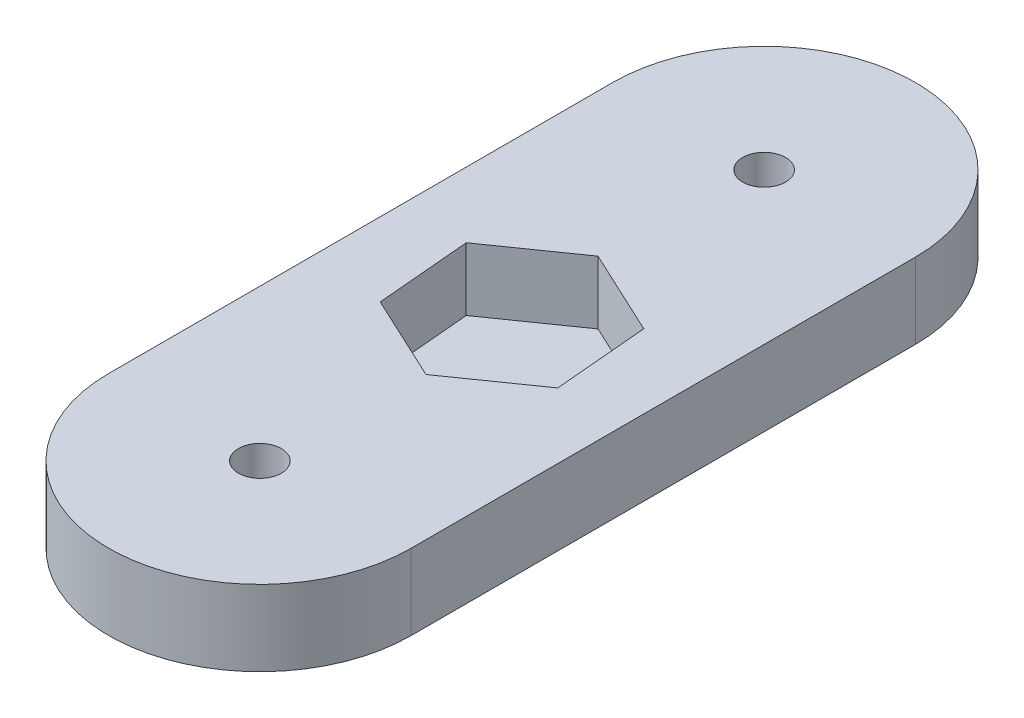
SolidWorks part; units mm, degrees
material "ABS PC"
ref_plane "Front Plane" through (0, 0, 0) normal (0, 0, 1) x (1, 0, 0)
ref_plane "Top Plane" through (0, 0, 0) normal (0, 1, 0) x (1, 0, 0)
ref_plane "Right Plane" through (0, 0, 0) normal (1, 0, 0) x (0, 0, -1)
sketch "Sketch1" plane through (0, 0, 0) normal (0, 1, 0) x (1, 0, 0)
  line L0 (0, 0) -> (0, 40) construction
  line L1 (-12, 0) -> (-12, 40)
  line L2 (12, 0) -> (12, 40)
  arc A0 (-12, 0) -> (12, 0) centre (0, 0) ccw
  arc A1 (12, 40) -> (-12, 40) centre (0, 40) ccw
  circle A2 centre (0, 40) radius 1.7
  circle A3 centre (0, 0) radius 1.7
  point P3 (0, 20)
  dimension "D2" = 40
  dimension "D3" = 3.4
  dimension "D1" = 24
extrude "Boss-Extrude1" add sketch "Sketch1" along normal blind 6
sketch "Sketch2" plane through (0, 6, 0) normal (0, 1, 0) x (1, 0, 0)
  line L0 (12, 0) -> (12, 40) construction
  line L1 (0.6542, 12.523) -> (6.8023, 16.828)
  line L2 (6.8023, 16.828) -> (6.1482, 24.305)
  line L3 (6.1482, 24.305) -> (-0.6542, 27.477)
  line L4 (-0.6542, 27.477) -> (-6.8023, 23.172)
  line L5 (-6.8023, 23.172) -> (-6.1482, 15.695)
  line L6 (-6.1482, 15.695) -> (0.6542, 12.523)
  line L7 (-12, 40) -> (-12, 0) construction
  circle A0 centre (0, 20) radius 6.5 construction
  dimension "D1" = 13
  dimension "D2" = 12
  dimension "D3" = 20
  dimension "D4" = 65
extrude "Cut-Extrude1" cut sketch "Sketch2" against normal blind 5
